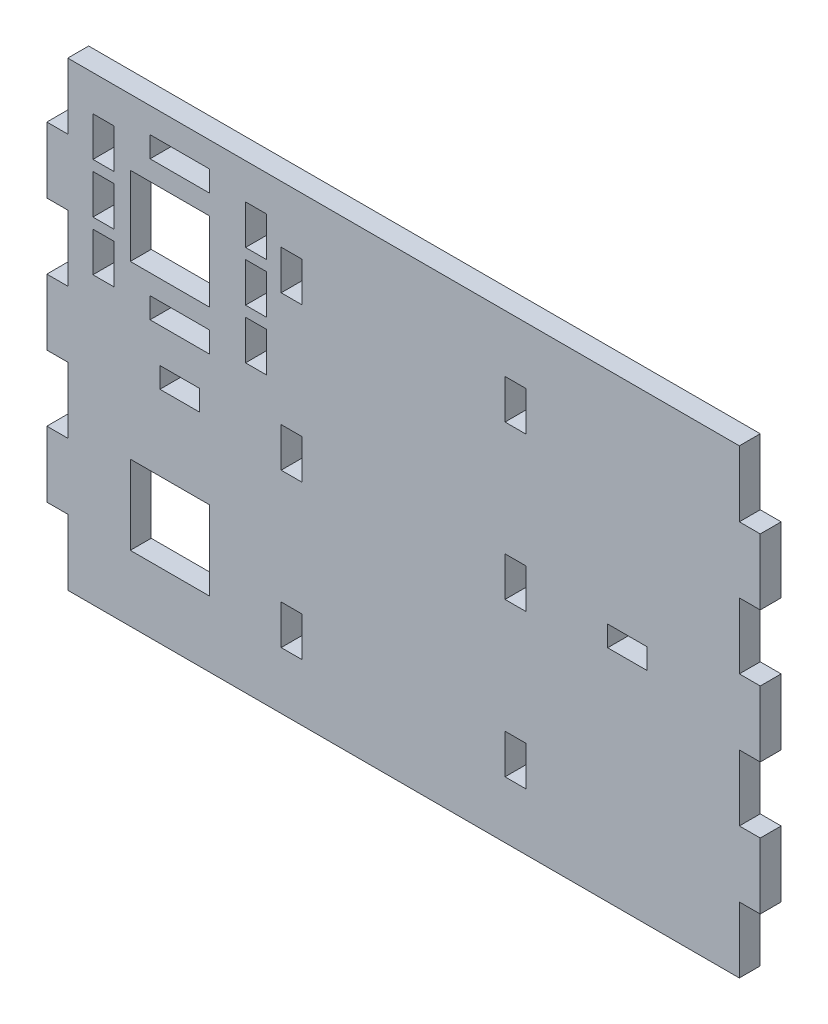
SolidWorks part; units mm, degrees
ref_plane "Front Plane" through (0, 0, 0) normal (0, 0, 1) x (1, 0, 0)
ref_plane "Top Plane" through (0, 0, 0) normal (0, 1, 0) x (1, 0, 0)
ref_plane "Right Plane" through (0, 0, 0) normal (1, 0, 0) x (0, 0, -1)
sketch "Sketch1" plane through (0, 0, 0) normal (0, 0, 1) x (1, 0, 0)
  line L0 (54.175, 5) -> (54.175, -5)
  line L1 (54.175, -25) -> (51, -25)
  line L2 (54.175, -15) -> (54.175, -25)
  line L3 (-51, 35) -> (-51, 25)
  line L4 (-51, 35) -> (51, 35)
  line L5 (0, 16.6227) -> (0, 8.5774) construction
  line L6 (23.0942, 0) -> (-1.5596, 0) construction
  line L7 (51, 25) -> (51, 35)
  line L8 (54.175, 5) -> (51, 5)
  line L9 (51, -15) -> (54.175, -15)
  line L10 (51, -5) -> (51, -15)
  line L11 (51, -25) -> (51, -35)
  line L12 (-51, -35) -> (51, -35)
  line L13 (-51, -25) -> (-51, -35)
  line L14 (54.175, -5) -> (51, -5)
  line L15 (-34, 35) -> (-34, -35) construction
  line L16 (-29.5, 31.175) -> (-38.5, 31.175)
  line L17 (-29.5, 31.175) -> (-29.5, 28)
  line L18 (-29.5, 28) -> (-34, 28)
  line L19 (-34, 28) -> (-38.5, 28)
  line L20 (-38.5, 28) -> (-38.5, 31.175)
  line L21 (-38.5, 10) -> (-38.5, 6.825)
  line L22 (-34, 25) -> (-29.5, 25)
  line L23 (-29.5, 25) -> (-29.5, 13)
  line L24 (-51, 35) -> (0, 35)
  line L25 (54.175, 0) -> (37, 0) construction
  line L26 (37, 1.5625) -> (31, 1.5625)
  line L27 (31, 1.5625) -> (31, -1.5625)
  line L28 (37, 1.5625) -> (37, -1.5625)
  line L29 (37, 0) -> (54.175, 0)
  line L30 (37, -1.5625) -> (31, -1.5625)
  line L31 (-37, -1.5625) -> (-31, -1.5625)
  line L32 (-37, 1.5625) -> (-37, -1.5625)
  line L33 (-31, 1.5625) -> (-31, -1.5625)
  line L34 (31, 0) -> (9.8, 0) construction
  line L35 (34, 1.5625) -> (34, 7.6646) construction
  line L36 (-51, 35) -> (0, 35)
  line L37 (18.5875, -3) -> (18.5875, 3)
  line L38 (18.5875, 3) -> (15.4125, 3)
  line L39 (15.4125, 3) -> (15.4125, -3)
  line L40 (17, 3) -> (17, 12.6102) construction
  line L41 (18.5875, -3) -> (15.4125, -3)
  line L42 (-18.5875, -3) -> (-15.4125, -3)
  line L43 (-15.4125, 3) -> (-15.4125, -3)
  line L44 (0, -35) -> (51, -35)
  line L45 (-17, 35) -> (-17, -35) construction
  line L46 (0, -35) -> (-51, -35)
  line L47 (0, 35) -> (51, 35)
  line L48 (17, 35) -> (17, -35) construction
  line L49 (-54.175, 25) -> (-51, 25)
  line L50 (-54.175, 15) -> (-54.175, 25)
  line L51 (-51, 15) -> (-54.175, 15)
  line L52 (-51, 5) -> (-51, 15)
  line L53 (51, 5) -> (51, 15)
  line L54 (51, 15) -> (54.175, 15)
  line L55 (54.175, 15) -> (54.175, 25)
  line L56 (54.175, 25) -> (51, 25)
  line L57 (-54.175, -5) -> (-51, -5)
  line L58 (-51, -5) -> (-51, -15)
  line L59 (-51, -15) -> (-54.175, -15)
  line L60 (-54.175, 5) -> (-51, 5)
  line L61 (-54.175, -15) -> (-54.175, -25)
  line L62 (-54.175, -25) -> (-51, -25)
  line L63 (-54.175, 5) -> (-54.175, -5)
  line L64 (55, 0) -> (-55, 0) construction
  line L65 (0, -55) -> (0, 55) construction
  line L66 (-37, 1.5625) -> (-31, 1.5625)
  line L67 (-29.5, 13) -> (-41.5, 13)
  line L68 (-34, 10) -> (-38.5, 10)
  line L69 (-41.5, 13) -> (-41.5, 25)
  line L70 (-17, 35) -> (17, 35)
  line L71 (17, 35) -> (51, 35)
  line L72 (-51, 35) -> (-17, 35)
  line L73 (17, 35) -> (51, 35)
  line L74 (-41.5, 25) -> (-34, 25)
  line L75 (-18.5875, 3) -> (-15.4125, 3)
  line L76 (34, 35) -> (34, -35) construction
  line L77 (-18.5875, -3) -> (-18.5875, 3)
  line L78 (-17, 35) -> (-17, 11.6667) construction
  line L79 (-17, 11.6667) -> (-17, -11.6667) construction
  line L80 (-17, -11.6667) -> (-17, -35) construction
  line L81 (-17, 20.3333) -> (-17, 23.3333) construction
  line L82 (-18.5875, 23.3333) -> (-18.5875, 26.3333)
  line L83 (-18.5875, 26.3333) -> (-15.4125, 26.3333)
  line L84 (-17, 23.3333) -> (-18.5875, 23.3333) construction
  line L85 (-15.4125, 26.3333) -> (-15.4125, 20.3333)
  line L86 (-15.4125, 20.3333) -> (-18.5875, 20.3333)
  line L87 (-18.5875, 20.3333) -> (-18.5875, 23.3333)
  line L88 (17, 23.3333) -> (18.5875, 23.3333) construction
  line L89 (17, 20.3333) -> (17, 23.3333) construction
  line L90 (18.5875, 20.3333) -> (18.5875, 23.3333)
  line L91 (15.4125, 20.3333) -> (18.5875, 20.3333)
  line L92 (15.4125, 26.3333) -> (15.4125, 20.3333)
  line L93 (18.5875, 26.3333) -> (15.4125, 26.3333)
  line L94 (18.5875, 23.3333) -> (18.5875, 26.3333)
  line L95 (17, -20.3333) -> (17, -23.3333) construction
  line L96 (17, -23.3333) -> (18.5875, -23.3333) construction
  line L97 (18.5875, -23.3333) -> (18.5875, -26.3333)
  line L98 (18.5875, -26.3333) -> (15.4125, -26.3333)
  line L99 (15.4125, -26.3333) -> (15.4125, -20.3333)
  line L100 (15.4125, -20.3333) -> (18.5875, -20.3333)
  line L101 (18.5875, -20.3333) -> (18.5875, -23.3333)
  line L102 (-17, -23.3333) -> (-18.5875, -23.3333) construction
  line L103 (-17, -20.3333) -> (-17, -23.3333) construction
  line L104 (-18.5875, -20.3333) -> (-18.5875, -23.3333)
  line L105 (-15.4125, -20.3333) -> (-18.5875, -20.3333)
  line L106 (-15.4125, -26.3333) -> (-15.4125, -20.3333)
  line L107 (-18.5875, -26.3333) -> (-15.4125, -26.3333)
  line L108 (-18.5875, -23.3333) -> (-18.5875, -26.3333)
  line L109 (-2.5481, 19) -> (-5.0089, 19) construction
  line L110 (-44, 19) -> (-44, 22)
  line L111 (-44, 22) -> (-47.175, 22)
  line L112 (-47.175, 22) -> (-47.175, 16)
  line L113 (-47.175, 16) -> (-44, 16)
  line L114 (-44, 16) -> (-44, 19)
  line L115 (-44, 23.5875) -> (-44, 29.5875)
  line L116 (-44, 29.5875) -> (-47.175, 29.5875)
  line L117 (-47.175, 29.5875) -> (-47.175, 23.5875)
  line L118 (-47.175, 23.5875) -> (-44, 23.5875)
  line L119 (-44, 14.4125) -> (-47.175, 14.4125)
  line L120 (-47.175, 14.4125) -> (-47.175, 8.4125)
  line L121 (-47.175, 8.4125) -> (-44, 8.4125)
  line L122 (-44, 8.4125) -> (-44, 14.4125)
  line L123 (-45.5875, 22) -> (-45.5875, 23.5875)
  line L124 (-45.5875, 16) -> (-45.5875, 14.4125)
  line L125 (-29.5, 10) -> (-34, 10)
  line L126 (-29.5, 6.825) -> (-29.5, 10)
  line L127 (-29.5, 6.825) -> (-38.5, 6.825)
  line L128 (-22.4125, 16) -> (-22.4125, 14.4125)
  line L129 (-22.4125, 22) -> (-22.4125, 23.5875)
  line L130 (-24, 8.4125) -> (-24, 14.4125)
  line L131 (-20.825, 8.4125) -> (-24, 8.4125)
  line L132 (-20.825, 14.4125) -> (-20.825, 8.4125)
  line L133 (-24, 14.4125) -> (-20.825, 14.4125)
  line L134 (-20.825, 23.5875) -> (-24, 23.5875)
  line L135 (-20.825, 29.5875) -> (-20.825, 23.5875)
  line L136 (-24, 29.5875) -> (-20.825, 29.5875)
  line L137 (-24, 23.5875) -> (-24, 29.5875)
  line L138 (-24, 16) -> (-24, 19)
  line L139 (-20.825, 16) -> (-24, 16)
  line L140 (-20.825, 22) -> (-20.825, 16)
  line L141 (-24, 22) -> (-20.825, 22)
  line L142 (-24, 19) -> (-24, 22)
  line L143 (-41.5, 19) -> (-1.5127, 19) construction
  line L144 (-41.5, 13) -> (-34, 13)
  line L145 (-29.5, 25) -> (-41.5, 25)
  line L146 (-34, 13) -> (-29.5, 13)
  line L147 (-34, 25) -> (-29.5, 25)
  line L148 (-29.5, 13) -> (-41.5, 13)
  line L149 (-41.5, 25) -> (-34, 25)
  line L150 (-41.5, 13) -> (-34, 13)
  line L151 (-29.5, 25) -> (-41.5, 25)
  line L152 (-34, 13) -> (-29.5, 13)
  line L153 (-51, 35) -> (-17, 35)
  line L154 (-34, -13) -> (-29.5, -13)
  line L155 (-29.5, -25) -> (-41.5, -25)
  line L156 (-41.5, -13) -> (-34, -13)
  line L157 (-41.5, -25) -> (-34, -25)
  line L158 (-29.5, -13) -> (-41.5, -13)
  line L159 (-34, -25) -> (-29.5, -25)
  line L160 (-34, -13) -> (-29.5, -13)
  line L161 (-29.5, -25) -> (-41.5, -25)
  line L162 (-41.5, -13) -> (-34, -13)
  line L163 (-41.5, -25) -> (-34, -25)
  line L164 (-41.5, -13) -> (-41.5, -25)
  line L165 (-29.5, -13) -> (-41.5, -13)
  line L166 (-29.5, -25) -> (-29.5, -13)
  line L167 (-34, -25) -> (-29.5, -25)
  line L168 (-34, 35) -> (-34, -35) construction
  point P0 (-2.7216, -35)
  point P17 (81.35, 0)
  point P22 (-81.35, 0)
  point P60 (15.4125, 0)
  point P89 (18.5875, 0)
  point P93 (-18.5875, 0)
  point P94 (-15.4125, 0)
  dimension "D2" = 6
  dimension "D3" = 3.175
  dimension "D4" = 102
  dimension "D5" = 12
  dimension "D6" = 4.5
  dimension "D7" = 6
  dimension "D8" = 1.5625
  dimension "D9" = 3.175
  dimension "D10" = 3
  dimension "D11" = 9
  dimension "D12" = 12
  dimension "D13" = 1.5875
  dimension "D14" = 3.175
  dimension "D15" = 70
  dimension "D16" = 20
  dimension "D17" = 3.175
  dimension "D18" = 18
extrude "Boss-Extrude1" add sketch "Sketch1" along normal mid plane 3.175
